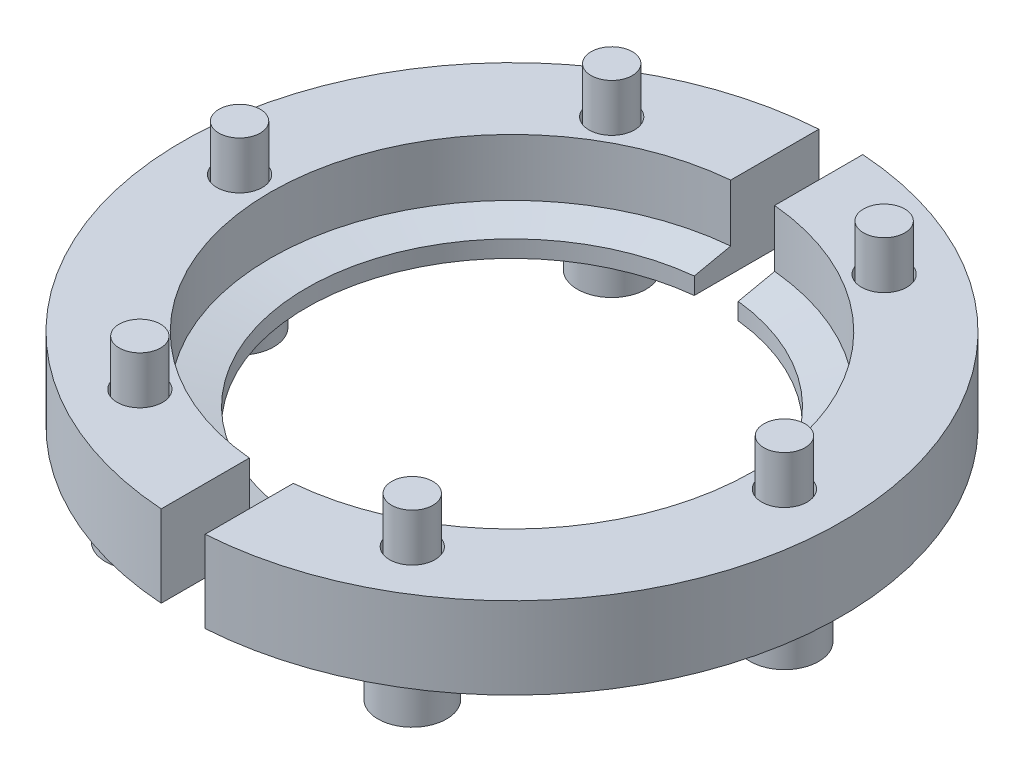
SolidWorks part; units mm, degrees
material "6061-T6 (SS)"
ref_plane "Front Plane" through (0, 0, 0) normal (0, 0, 1) x (1, 0, 0)
ref_plane "Top Plane" through (0, 0, 0) normal (0, 1, 0) x (1, 0, 0)
ref_plane "Right Plane" through (0, 0, 0) normal (1, 0, 0) x (0, 0, -1)
sketch "Sketch1" plane through (0, 0, 0) normal (0, 1, 0) x (1, 0, 0)
  circle A0 centre (0, 0) radius 37.5
  dimension "D1" = 75
extrude "Boss-Extrude1" add sketch "Sketch1" along normal blind 9.3
sketch "Sketch2" plane through (0, 0, 0) normal (0, 0, 1) x (1, 0, 0)
  line L0 (23.375, 0) -> (23.375, 1.9232)
  line L1 (-37.5, 0) -> (37.5, 0) construction
  line L2 (23.375, 1.9232) -> (27.5, 2.8)
  line L3 (27.5, 2.8) -> (27.5, 9.3)
  line L4 (37.5, 9.3) -> (-37.5, 9.3) construction
  line L5 (27.5, 9.3) -> (0, 9.3)
  line L6 (0, 9.3) -> (0, 0)
  line L7 (0, 0) -> (23.375, 0)
  line L8 (0, 0) -> (0, -3.744) construction
  dimension "D1" = 55
  dimension "D2" = 6.5
  dimension "D3" = 46.75
  dimension "D4" = 78
revolve "Cut-Revolve1" cut sketch "Sketch2" angle 360 about L8
sketch "Sketch3" plane through (0, 9.3, 0) normal (0, 1, 0) x (1, 0, 0)
  line L0 (0, 0) -> (0, -3.5728) construction
  circle A0 centre (31, 0) radius 2.585
  dimension "D1" = 62
  dimension "D2" = 5.17
extrude "Cut-Extrude1" cut sketch "Sketch3" against normal through all
pattern_circular "CirPattern1" count 6 over 360 about axis through (0, 0, 0) along (0, 1, 0) of "Cut-Extrude1"
sketch "Sketch4" plane through (0, 9.3, 0) normal (0, 1, 0) x (1, 0, 0)
  line L0 (-2.5, 37.4166) -> (-2.5, -37.4166)
  line L1 (2.5, -37.4166) -> (2.5, 37.4166)
  line L2 (0, 0) -> (0, 6.0027) construction
  line L3 (0, 6.0027) -> (2.5, 6.0027) construction
  line L4 (0, 6.0027) -> (-2.5, 6.0027) construction
  line L5 (0, 0) -> (11.0132, 0) construction
  circle A0 centre (0, 0) radius 37.5 construction
  arc A1 (-2.5, -37.4166) -> (2.5, -37.4166) centre (0, 0) ccw
  arc A2 (2.5, 37.4166) -> (-2.5, 37.4166) centre (0, 0) ccw
  dimension "D1" = 5
  dimension "D2" = 90
extrude "Cut-Extrude2" cut sketch "Sketch4" against normal through all
sketch "Sketch5" plane through (0, 0, 0) normal (0, -1, 0) x (1, 0, 0)
  circle A0 centre (31, 0) radius 2.7
  circle A1 centre (31, 0) radius 4.93
  dimension "D1" = 5.4
  dimension "D2" = 9.86
extrude "Boss-Extrude2" add sketch "Sketch5" along normal blind 0.95 separate body
sketch "Sketch7" plane through (0, 0, 0) normal (0, 0, 1) x (1, 0, 0)
  line L0 (31, -0.95) -> (31, 14.55) construction
  line L1 (26.07, -0.95) -> (35.93, -0.95) construction
  line L2 (31, 14.55) -> (33.35, 14.55)
  line L3 (33.35, 14.55) -> (33.35, -0.95)
  line L4 (33.35, -0.95) -> (34.9, -0.95)
  line L5 (34.9, -0.95) -> (34.9, -5.75)
  line L6 (34.9, -5.75) -> (31, -5.75)
  line L7 (31, -5.75) -> (31, 14.55)
  line L8 (31, 14.55) -> (31, 17.1971) construction
  dimension "D1" = 4.8
  dimension "D2" = 7.8
  dimension "D3" = 4.7
  dimension "D4" = 20.3
revolve "Revolve1" add sketch "Sketch7" angle 360 about L8
sketch "Sketch8" plane through (0, -5.75, 0) normal (0, -1, 0) x (1, 0, 0)
  line L1 (31, 2.3383) -> (28.975, 1.1691)
  line L2 (28.975, 1.1691) -> (28.975, -1.1691)
  line L3 (28.975, -1.1691) -> (31, -2.3383)
  line L4 (31, -2.3383) -> (33.025, -1.1691)
  line L5 (33.025, -1.1691) -> (33.025, 1.1691)
  line L6 (33.025, 1.1691) -> (31, 2.3383)
  circle A0 centre (31, 0) radius 2.025 construction
  dimension "D1" = 4.05
extrude "Cut-Extrude3" cut sketch "Sketch8" against normal blind 3.2
pattern_circular "CirPattern2" count 6 over 360 about axis through (0, 0, 0) along (0, 1, 0) of bodies 112 114
ref_plane "Plane1" through (0, 7.8, 0) normal (0, 1, 0) x (1, 0, 0)
